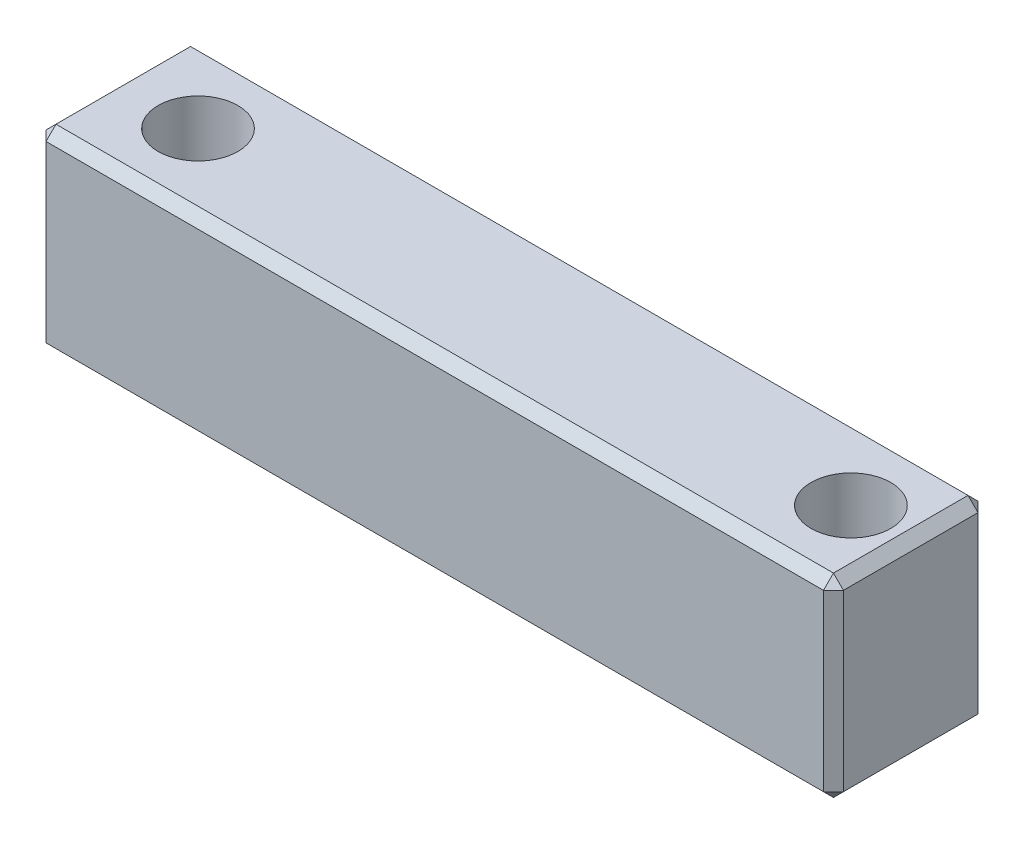
SolidWorks part; units mm, degrees
ref_plane "Front Plane" through (0, 0, 0) normal (0, 0, 1) x (1, 0, 0)
ref_plane "Top Plane" through (0, 0, 0) normal (0, 1, 0) x (1, 0, 0)
ref_plane "Right Plane" through (0, 0, 0) normal (1, 0, 0) x (0, 0, -1)
sketch "Sketch1" plane through (0, 0, 0) normal (1, 0, 0) x (0, 0, -1)
  line L1 (0, 0) -> (7.75, 0)
  line L2 (0, 0) -> (0, 9.75)
  line L3 (0, 9.75) -> (7.75, 9.75)
  line L4 (7.75, 0) -> (7.75, 9.75)
  dimension "D1" = 7.75
  dimension "D2" = 9.75
extrude "Boss-Extrude1" add sketch "Sketch1" along normal blind 40
sketch "Sketch4" plane through (0, 9.75, 0) normal (0, 1, 0) x (1, 0, 0)
  line L0 (0, 3.875) -> (4.25, 3.875) construction
  line L1 (0, 7.75) -> (0, 0) construction
  line L2 (40, 3.875) -> (37, 3.875) construction
  line L3 (40, 7.75) -> (40, 0) construction
  circle A2 centre (4.25, 3.875) radius 2
  circle A3 centre (37, 3.875) radius 2
  dimension "D2" = 3
  dimension "D1" = 4.25
extrude "Cut-Extrude3" cut sketch "Sketch4" against normal up to surface (9.75 mm away) up to face at (20, 0, -3.875)
chamfer "Chamfer1" distance 0.5 angle 45 12 edges at (40, 4.875, 0) (40, 9.75, -3.875) (20, 9.75, 0) (0, 9.75, -3.875) (0, 4.875, 0) (20, 0, 0) (40, 0, -3.875) (0, 0, -3.875) (20, 0, -7.75) (40, 4.875, -7.75) (20, 9.75, -7.75) (0, 4.875, -7.75)
